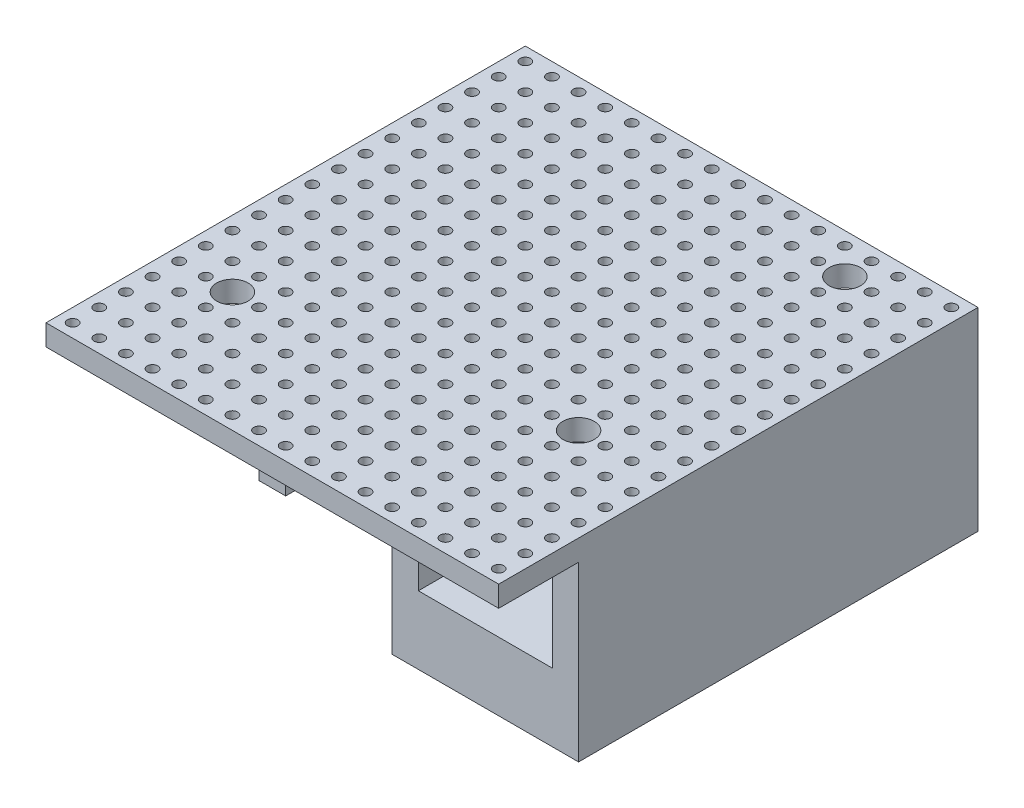
SolidWorks part; units mm, degrees
ref_plane "Front Plane" through (0, 0, 0) normal (0, 0, 1) x (1, 0, 0)
ref_plane "Top Plane" through (0, 0, 0) normal (0, 1, 0) x (1, 0, 0)
ref_plane "Right Plane" through (0, 0, 0) normal (1, 0, 0) x (0, 0, -1)
sketch "Sketch1" plane through (0, 0, 0) normal (0, 1, 0) x (1, 0, 0)
  line L1 (-28.6326, 15.7481) -> (34.8674, 15.7481)
  line L2 (-28.6326, 15.7481) -> (-28.6326, -29.9719)
  line L3 (-28.6326, -29.9719) -> (34.8674, -29.9719)
  line L4 (34.8674, 15.7481) -> (34.8674, -29.9719)
  circle A0 centre (33.5974, -28.7019) radius 0.5
  circle A1 centre (31.0574, -28.7019) radius 0.5
  circle A2 centre (28.5174, -28.7019) radius 0.5
  circle A3 centre (25.9774, -28.7019) radius 0.5
  circle A4 centre (23.4374, -28.7019) radius 0.5
  circle A5 centre (20.8974, -28.7019) radius 0.5
  circle A6 centre (18.3574, -28.7019) radius 0.5
  circle A7 centre (15.8174, -28.7019) radius 0.5
  circle A8 centre (13.2774, -28.7019) radius 0.5
  circle A9 centre (10.7374, -28.7019) radius 0.5
  circle A10 centre (8.1974, -28.7019) radius 0.5
  circle A11 centre (5.6574, -28.7019) radius 0.5
  circle A12 centre (3.1174, -28.7019) radius 0.5
  circle A13 centre (0.5774, -28.7019) radius 0.5
  circle A14 centre (-1.9626, -28.7019) radius 0.5
  circle A15 centre (-4.5026, -28.7019) radius 0.5
  circle A16 centre (-7.0426, -28.7019) radius 0.5
  circle A17 centre (-9.5826, -28.7019) radius 0.5
  circle A18 centre (-12.1226, -28.7019) radius 0.5
  circle A19 centre (-14.6626, -28.7019) radius 0.5
  circle A20 centre (-17.2026, -28.7019) radius 0.5
  circle A21 centre (-19.7426, -28.7019) radius 0.5
  circle A22 centre (-22.2826, -28.7019) radius 0.5
  circle A23 centre (-24.8226, -28.7019) radius 0.5
  circle A24 centre (-27.3626, -28.7019) radius 0.5
  circle A25 centre (31.0574, -26.1619) radius 0.5
  circle A26 centre (28.5174, -26.1619) radius 0.5
  circle A27 centre (25.9774, -26.1619) radius 0.5
  circle A28 centre (23.4374, -26.1619) radius 0.5
  circle A29 centre (20.8974, -26.1619) radius 0.5
  circle A30 centre (18.3574, -26.1619) radius 0.5
  circle A31 centre (15.8174, -26.1619) radius 0.5
  circle A32 centre (13.2774, -26.1619) radius 0.5
  circle A33 centre (10.7374, -26.1619) radius 0.5
  circle A34 centre (8.1974, -26.1619) radius 0.5
  circle A35 centre (5.6574, -26.1619) radius 0.5
  circle A36 centre (3.1174, -26.1619) radius 0.5
  circle A37 centre (0.5774, -26.1619) radius 0.5
  circle A38 centre (-1.9626, -26.1619) radius 0.5
  circle A39 centre (-4.5026, -26.1619) radius 0.5
  circle A40 centre (-7.0426, -26.1619) radius 0.5
  circle A41 centre (-9.5826, -26.1619) radius 0.5
  circle A42 centre (-12.1226, -26.1619) radius 0.5
  circle A43 centre (-14.6626, -26.1619) radius 0.5
  circle A44 centre (-17.2026, -26.1619) radius 0.5
  circle A45 centre (-19.7426, -26.1619) radius 0.5
  circle A46 centre (-22.2826, -26.1619) radius 0.5
  circle A47 centre (-24.8226, -26.1619) radius 0.5
  circle A48 centre (-27.3626, -26.1619) radius 0.5
  circle A49 centre (31.0574, -23.6219) radius 0.5
  circle A50 centre (28.5174, -23.6219) radius 0.5
  circle A51 centre (25.9774, -23.6219) radius 0.5
  circle A52 centre (23.4374, -23.6219) radius 0.5
  circle A53 centre (20.8974, -23.6219) radius 0.5
  circle A54 centre (18.3574, -23.6219) radius 0.5
  circle A55 centre (15.8174, -23.6219) radius 0.5
  circle A56 centre (13.2774, -23.6219) radius 0.5
  circle A57 centre (10.7374, -23.6219) radius 0.5
  circle A58 centre (8.1974, -23.6219) radius 0.5
  circle A59 centre (5.6574, -23.6219) radius 0.5
  circle A60 centre (3.1174, -23.6219) radius 0.5
  circle A61 centre (0.5774, -23.6219) radius 0.5
  circle A62 centre (-1.9626, -23.6219) radius 0.5
  circle A63 centre (-4.5026, -23.6219) radius 0.5
  circle A64 centre (-7.0426, -23.6219) radius 0.5
  circle A65 centre (-9.5826, -23.6219) radius 0.5
  circle A66 centre (-12.1226, -23.6219) radius 0.5
  circle A67 centre (-14.6626, -23.6219) radius 0.5
  circle A68 centre (-17.2026, -23.6219) radius 0.5
  circle A69 centre (-19.7426, -23.6219) radius 0.5
  circle A70 centre (-22.2826, -23.6219) radius 0.5
  circle A71 centre (-24.8226, -23.6219) radius 0.5
  circle A72 centre (-27.3626, -23.6219) radius 0.5
  circle A73 centre (31.0574, -21.0819) radius 0.5
  circle A74 centre (28.5174, -21.0819) radius 0.5
  circle A75 centre (25.9774, -21.0819) radius 0.5
  circle A76 centre (23.4374, -21.0819) radius 0.5
  circle A77 centre (20.8974, -21.0819) radius 0.5
  circle A78 centre (18.3574, -21.0819) radius 0.5
  circle A79 centre (15.8174, -21.0819) radius 0.5
  circle A80 centre (13.2774, -21.0819) radius 0.5
  circle A81 centre (10.7374, -21.0819) radius 0.5
  circle A82 centre (8.1974, -21.0819) radius 0.5
  circle A83 centre (5.6574, -21.0819) radius 0.5
  circle A84 centre (3.1174, -21.0819) radius 0.5
  circle A85 centre (0.5774, -21.0819) radius 0.5
  circle A86 centre (-1.9626, -21.0819) radius 0.5
  circle A87 centre (-4.5026, -21.0819) radius 0.5
  circle A88 centre (-7.0426, -21.0819) radius 0.5
  circle A89 centre (-9.5826, -21.0819) radius 0.5
  circle A90 centre (-12.1226, -21.0819) radius 0.5
  circle A91 centre (-14.6626, -21.0819) radius 0.5
  circle A92 centre (-17.2026, -21.0819) radius 0.5
  circle A93 centre (-19.7426, -21.0819) radius 0.5
  circle A94 centre (-22.2826, -21.0819) radius 0.5
  circle A95 centre (-24.8226, -21.0819) radius 0.5
  circle A96 centre (-27.3626, -21.0819) radius 0.5
  circle A97 centre (31.0574, -18.5419) radius 0.5
  circle A98 centre (28.5174, -18.5419) radius 0.5
  circle A99 centre (25.9774, -18.5419) radius 0.5
  circle A100 centre (23.4374, -18.5419) radius 0.5
  circle A101 centre (20.8974, -18.5419) radius 0.5
  circle A102 centre (18.3574, -18.5419) radius 0.5
  circle A103 centre (15.8174, -18.5419) radius 0.5
  circle A104 centre (13.2774, -18.5419) radius 0.5
  circle A105 centre (10.7374, -18.5419) radius 0.5
  circle A106 centre (8.1974, -18.5419) radius 0.5
  circle A107 centre (5.6574, -18.5419) radius 0.5
  circle A108 centre (3.1174, -18.5419) radius 0.5
  circle A109 centre (0.5774, -18.5419) radius 0.5
  circle A110 centre (-1.9626, -18.5419) radius 0.5
  circle A111 centre (-4.5026, -18.5419) radius 0.5
  circle A112 centre (-7.0426, -18.5419) radius 0.5
  circle A113 centre (-9.5826, -18.5419) radius 0.5
  circle A114 centre (-12.1226, -18.5419) radius 0.5
  circle A115 centre (-14.6626, -18.5419) radius 0.5
  circle A116 centre (-17.2026, -18.5419) radius 0.5
  circle A117 centre (-19.7426, -18.5419) radius 0.5
  circle A118 centre (-22.2826, -18.5419) radius 0.5
  circle A119 centre (-24.8226, -18.5419) radius 0.5
  circle A120 centre (-27.3626, -18.5419) radius 0.5
  circle A121 centre (31.0574, -16.0019) radius 0.5
  circle A122 centre (28.5174, -16.0019) radius 0.5
  circle A123 centre (25.9774, -16.0019) radius 0.5
  circle A124 centre (23.4374, -16.0019) radius 0.5
  circle A125 centre (20.8974, -16.0019) radius 0.5
  circle A126 centre (18.3574, -16.0019) radius 0.5
  circle A127 centre (15.8174, -16.0019) radius 0.5
  circle A128 centre (13.2774, -16.0019) radius 0.5
  circle A129 centre (10.7374, -16.0019) radius 0.5
  circle A130 centre (8.1974, -16.0019) radius 0.5
  circle A131 centre (5.6574, -16.0019) radius 0.5
  circle A132 centre (3.1174, -16.0019) radius 0.5
  circle A133 centre (0.5774, -16.0019) radius 0.5
  circle A134 centre (-1.9626, -16.0019) radius 0.5
  circle A135 centre (-4.5026, -16.0019) radius 0.5
  circle A136 centre (-7.0426, -16.0019) radius 0.5
  circle A137 centre (-9.5826, -16.0019) radius 0.5
  circle A138 centre (-12.1226, -16.0019) radius 0.5
  circle A139 centre (-14.6626, -16.0019) radius 0.5
  circle A140 centre (-17.2026, -16.0019) radius 0.5
  circle A141 centre (-19.7426, -16.0019) radius 0.5
  circle A142 centre (-22.2826, -16.0019) radius 0.5
  circle A143 centre (-24.8226, -16.0019) radius 0.5
  circle A144 centre (-27.3626, -16.0019) radius 0.5
  circle A145 centre (31.0574, -13.4619) radius 0.5
  circle A146 centre (28.5174, -13.4619) radius 0.5
  circle A147 centre (25.9774, -13.4619) radius 0.5
  circle A148 centre (23.4374, -13.4619) radius 0.5
  circle A149 centre (20.8974, -13.4619) radius 0.5
  circle A150 centre (18.3574, -13.4619) radius 0.5
  circle A151 centre (15.8174, -13.4619) radius 0.5
  circle A152 centre (13.2774, -13.4619) radius 0.5
  circle A153 centre (10.7374, -13.4619) radius 0.5
  circle A154 centre (8.1974, -13.4619) radius 0.5
  circle A155 centre (5.6574, -13.4619) radius 0.5
  circle A156 centre (3.1174, -13.4619) radius 0.5
  circle A157 centre (0.5774, -13.4619) radius 0.5
  circle A158 centre (-1.9626, -13.4619) radius 0.5
  circle A159 centre (-4.5026, -13.4619) radius 0.5
  circle A160 centre (-7.0426, -13.4619) radius 0.5
  circle A161 centre (-9.5826, -13.4619) radius 0.5
  circle A162 centre (-12.1226, -13.4619) radius 0.5
  circle A163 centre (-14.6626, -13.4619) radius 0.5
  circle A164 centre (-17.2026, -13.4619) radius 0.5
  circle A165 centre (-19.7426, -13.4619) radius 0.5
  circle A166 centre (-22.2826, -13.4619) radius 0.5
  circle A167 centre (-24.8226, -13.4619) radius 0.5
  circle A168 centre (-27.3626, -13.4619) radius 0.5
  circle A169 centre (31.0574, -10.9219) radius 0.5
  circle A170 centre (28.5174, -10.9219) radius 0.5
  circle A171 centre (25.9774, -10.9219) radius 0.5
  circle A172 centre (23.4374, -10.9219) radius 0.5
  circle A173 centre (20.8974, -10.9219) radius 0.5
  circle A174 centre (18.3574, -10.9219) radius 0.5
  circle A175 centre (15.8174, -10.9219) radius 0.5
  circle A176 centre (13.2774, -10.9219) radius 0.5
  circle A177 centre (10.7374, -10.9219) radius 0.5
  circle A178 centre (8.1974, -10.9219) radius 0.5
  circle A179 centre (5.6574, -10.9219) radius 0.5
  circle A180 centre (3.1174, -10.9219) radius 0.5
  circle A181 centre (0.5774, -10.9219) radius 0.5
  circle A182 centre (-1.9626, -10.9219) radius 0.5
  circle A183 centre (-4.5026, -10.9219) radius 0.5
  circle A184 centre (-7.0426, -10.9219) radius 0.5
  circle A185 centre (-9.5826, -10.9219) radius 0.5
  circle A186 centre (-12.1226, -10.9219) radius 0.5
  circle A187 centre (-14.6626, -10.9219) radius 0.5
  circle A188 centre (-17.2026, -10.9219) radius 0.5
  circle A189 centre (-19.7426, -10.9219) radius 0.5
  circle A190 centre (-22.2826, -10.9219) radius 0.5
  circle A191 centre (-24.8226, -10.9219) radius 0.5
  circle A192 centre (-27.3626, -10.9219) radius 0.5
  circle A193 centre (31.0574, -8.3819) radius 0.5
  circle A194 centre (28.5174, -8.3819) radius 0.5
  circle A195 centre (25.9774, -8.3819) radius 0.5
  circle A196 centre (23.4374, -8.3819) radius 0.5
  circle A197 centre (20.8974, -8.3819) radius 0.5
  circle A198 centre (18.3574, -8.3819) radius 0.5
  circle A199 centre (15.8174, -8.3819) radius 0.5
  circle A200 centre (13.2774, -8.3819) radius 0.5
  circle A201 centre (10.7374, -8.3819) radius 0.5
  circle A202 centre (8.1974, -8.3819) radius 0.5
  circle A203 centre (5.6574, -8.3819) radius 0.5
  circle A204 centre (3.1174, -8.3819) radius 0.5
  circle A205 centre (0.5774, -8.3819) radius 0.5
  circle A206 centre (-1.9626, -8.3819) radius 0.5
  circle A207 centre (-4.5026, -8.3819) radius 0.5
  circle A208 centre (-7.0426, -8.3819) radius 0.5
  circle A209 centre (-9.5826, -8.3819) radius 0.5
  circle A210 centre (-12.1226, -8.3819) radius 0.5
  circle A211 centre (-14.6626, -8.3819) radius 0.5
  circle A212 centre (-17.2026, -8.3819) radius 0.5
  circle A213 centre (-19.7426, -8.3819) radius 0.5
  circle A214 centre (-22.2826, -8.3819) radius 0.5
  circle A215 centre (-24.8226, -8.3819) radius 0.5
  circle A216 centre (-27.3626, -8.3819) radius 0.5
  circle A217 centre (31.0574, -5.8419) radius 0.5
  circle A218 centre (28.5174, -5.8419) radius 0.5
  circle A219 centre (25.9774, -5.8419) radius 0.5
  circle A220 centre (23.4374, -5.8419) radius 0.5
  circle A221 centre (20.8974, -5.8419) radius 0.5
  circle A222 centre (18.3574, -5.8419) radius 0.5
  circle A223 centre (15.8174, -5.8419) radius 0.5
  circle A224 centre (13.2774, -5.8419) radius 0.5
  circle A225 centre (10.7374, -5.8419) radius 0.5
  circle A226 centre (8.1974, -5.8419) radius 0.5
  circle A227 centre (5.6574, -5.8419) radius 0.5
  circle A228 centre (3.1174, -5.8419) radius 0.5
  circle A229 centre (0.5774, -5.8419) radius 0.5
  circle A230 centre (-1.9626, -5.8419) radius 0.5
  circle A231 centre (-4.5026, -5.8419) radius 0.5
  circle A232 centre (-7.0426, -5.8419) radius 0.5
  circle A233 centre (-9.5826, -5.8419) radius 0.5
  circle A234 centre (-12.1226, -5.8419) radius 0.5
  circle A235 centre (-14.6626, -5.8419) radius 0.5
  circle A236 centre (-17.2026, -5.8419) radius 0.5
  circle A237 centre (-19.7426, -5.8419) radius 0.5
  circle A238 centre (-22.2826, -5.8419) radius 0.5
  circle A239 centre (-24.8226, -5.8419) radius 0.5
  circle A240 centre (-27.3626, -5.8419) radius 0.5
  circle A241 centre (31.0574, -3.3019) radius 0.5
  circle A242 centre (28.5174, -3.3019) radius 0.5
  circle A243 centre (25.9774, -3.3019) radius 0.5
  circle A244 centre (23.4374, -3.3019) radius 0.5
  circle A245 centre (20.8974, -3.3019) radius 0.5
  circle A246 centre (18.3574, -3.3019) radius 0.5
  circle A247 centre (15.8174, -3.3019) radius 0.5
  circle A248 centre (13.2774, -3.3019) radius 0.5
  circle A249 centre (10.7374, -3.3019) radius 0.5
  circle A250 centre (8.1974, -3.3019) radius 0.5
  circle A251 centre (5.6574, -3.3019) radius 0.5
  circle A252 centre (3.1174, -3.3019) radius 0.5
  circle A253 centre (0.5774, -3.3019) radius 0.5
  circle A254 centre (-1.9626, -3.3019) radius 0.5
  circle A255 centre (-4.5026, -3.3019) radius 0.5
  circle A256 centre (-7.0426, -3.3019) radius 0.5
  circle A257 centre (-9.5826, -3.3019) radius 0.5
  circle A258 centre (-12.1226, -3.3019) radius 0.5
  circle A259 centre (-14.6626, -3.3019) radius 0.5
  circle A260 centre (-17.2026, -3.3019) radius 0.5
  circle A261 centre (-19.7426, -3.3019) radius 0.5
  circle A262 centre (-22.2826, -3.3019) radius 0.5
  circle A263 centre (-24.8226, -3.3019) radius 0.5
  circle A264 centre (-27.3626, -3.3019) radius 0.5
  circle A265 centre (31.0574, -0.7619) radius 0.5
  circle A266 centre (28.5174, -0.7619) radius 0.5
  circle A267 centre (25.9774, -0.7619) radius 0.5
  circle A268 centre (23.4374, -0.7619) radius 0.5
  circle A269 centre (20.8974, -0.7619) radius 0.5
  circle A270 centre (18.3574, -0.7619) radius 0.5
  circle A271 centre (15.8174, -0.7619) radius 0.5
  circle A272 centre (13.2774, -0.7619) radius 0.5
  circle A273 centre (10.7374, -0.7619) radius 0.5
  circle A274 centre (8.1974, -0.7619) radius 0.5
  circle A275 centre (5.6574, -0.7619) radius 0.5
  circle A276 centre (3.1174, -0.7619) radius 0.5
  circle A277 centre (0.5774, -0.7619) radius 0.5
  circle A278 centre (-1.9626, -0.7619) radius 0.5
  circle A279 centre (-4.5026, -0.7619) radius 0.5
  circle A280 centre (-7.0426, -0.7619) radius 0.5
  circle A281 centre (-9.5826, -0.7619) radius 0.5
  circle A282 centre (-12.1226, -0.7619) radius 0.5
  circle A283 centre (-14.6626, -0.7619) radius 0.5
  circle A284 centre (-17.2026, -0.7619) radius 0.5
  circle A285 centre (-19.7426, -0.7619) radius 0.5
  circle A286 centre (-22.2826, -0.7619) radius 0.5
  circle A287 centre (-24.8226, -0.7619) radius 0.5
  circle A288 centre (-27.3626, -0.7619) radius 0.5
  circle A289 centre (31.0574, 1.7781) radius 0.5
  circle A290 centre (28.5174, 1.7781) radius 0.5
  circle A291 centre (25.9774, 1.7781) radius 0.5
  circle A292 centre (23.4374, 1.7781) radius 0.5
  circle A293 centre (20.8974, 1.7781) radius 0.5
  circle A294 centre (18.3574, 1.7781) radius 0.5
  circle A295 centre (15.8174, 1.7781) radius 0.5
  circle A296 centre (13.2774, 1.7781) radius 0.5
  circle A297 centre (10.7374, 1.7781) radius 0.5
  circle A298 centre (8.1974, 1.7781) radius 0.5
  circle A299 centre (5.6574, 1.7781) radius 0.5
  circle A300 centre (3.1174, 1.7781) radius 0.5
  circle A301 centre (0.5774, 1.7781) radius 0.5
  circle A302 centre (-1.9626, 1.7781) radius 0.5
  circle A303 centre (-4.5026, 1.7781) radius 0.5
  circle A304 centre (-7.0426, 1.7781) radius 0.5
  circle A305 centre (-9.5826, 1.7781) radius 0.5
  circle A306 centre (-12.1226, 1.7781) radius 0.5
  circle A307 centre (-14.6626, 1.7781) radius 0.5
  circle A308 centre (-17.2026, 1.7781) radius 0.5
  circle A309 centre (-19.7426, 1.7781) radius 0.5
  circle A310 centre (-22.2826, 1.7781) radius 0.5
  circle A311 centre (-24.8226, 1.7781) radius 0.5
  circle A312 centre (-27.3626, 1.7781) radius 0.5
  circle A313 centre (31.0574, 4.3181) radius 0.5
  circle A314 centre (28.5174, 4.3181) radius 0.5
  circle A315 centre (25.9774, 4.3181) radius 0.5
  circle A316 centre (23.4374, 4.3181) radius 0.5
  circle A317 centre (20.8974, 4.3181) radius 0.5
  circle A318 centre (18.3574, 4.3181) radius 0.5
  circle A319 centre (15.8174, 4.3181) radius 0.5
  circle A320 centre (13.2774, 4.3181) radius 0.5
  circle A321 centre (10.7374, 4.3181) radius 0.5
  circle A322 centre (8.1974, 4.3181) radius 0.5
  circle A323 centre (5.6574, 4.3181) radius 0.5
  circle A324 centre (3.1174, 4.3181) radius 0.5
  circle A325 centre (0.5774, 4.3181) radius 0.5
  circle A326 centre (-1.9626, 4.3181) radius 0.5
  circle A327 centre (-4.5026, 4.3181) radius 0.5
  circle A328 centre (-7.0426, 4.3181) radius 0.5
  circle A329 centre (-9.5826, 4.3181) radius 0.5
  circle A330 centre (-12.1226, 4.3181) radius 0.5
  circle A331 centre (-14.6626, 4.3181) radius 0.5
  circle A332 centre (-17.2026, 4.3181) radius 0.5
  circle A333 centre (-19.7426, 4.3181) radius 0.5
  circle A334 centre (-22.2826, 4.3181) radius 0.5
  circle A335 centre (-24.8226, 4.3181) radius 0.5
  circle A336 centre (-27.3626, 4.3181) radius 0.5
  circle A337 centre (31.0574, 6.8581) radius 0.5
  circle A338 centre (28.5174, 6.8581) radius 0.5
  circle A339 centre (25.9774, 6.8581) radius 0.5
  circle A340 centre (23.4374, 6.8581) radius 0.5
  circle A341 centre (20.8974, 6.8581) radius 0.5
  circle A342 centre (18.3574, 6.8581) radius 0.5
  circle A343 centre (15.8174, 6.8581) radius 0.5
  circle A344 centre (13.2774, 6.8581) radius 0.5
  circle A345 centre (10.7374, 6.8581) radius 0.5
  circle A346 centre (8.1974, 6.8581) radius 0.5
  circle A347 centre (5.6574, 6.8581) radius 0.5
  circle A348 centre (3.1174, 6.8581) radius 0.5
  circle A349 centre (0.5774, 6.8581) radius 0.5
  circle A350 centre (-1.9626, 6.8581) radius 0.5
  circle A351 centre (-4.5026, 6.8581) radius 0.5
  circle A352 centre (-7.0426, 6.8581) radius 0.5
  circle A353 centre (-9.5826, 6.8581) radius 0.5
  circle A354 centre (-12.1226, 6.8581) radius 0.5
  circle A355 centre (-14.6626, 6.8581) radius 0.5
  circle A356 centre (-17.2026, 6.8581) radius 0.5
  circle A357 centre (-19.7426, 6.8581) radius 0.5
  circle A358 centre (-22.2826, 6.8581) radius 0.5
  circle A359 centre (-24.8226, 6.8581) radius 0.5
  circle A360 centre (-27.3626, 6.8581) radius 0.5
  circle A361 centre (31.0574, 9.3981) radius 0.5
  circle A362 centre (28.5174, 9.3981) radius 0.5
  circle A363 centre (25.9774, 9.3981) radius 0.5
  circle A364 centre (23.4374, 9.3981) radius 0.5
  circle A365 centre (20.8974, 9.3981) radius 0.5
  circle A366 centre (18.3574, 9.3981) radius 0.5
  circle A367 centre (15.8174, 9.3981) radius 0.5
  circle A368 centre (13.2774, 9.3981) radius 0.5
  circle A369 centre (10.7374, 9.3981) radius 0.5
  circle A370 centre (8.1974, 9.3981) radius 0.5
  circle A371 centre (5.6574, 9.3981) radius 0.5
  circle A372 centre (3.1174, 9.3981) radius 0.5
  circle A373 centre (0.5774, 9.3981) radius 0.5
  circle A374 centre (-1.9626, 9.3981) radius 0.5
  circle A375 centre (-4.5026, 9.3981) radius 0.5
  circle A376 centre (-7.0426, 9.3981) radius 0.5
  circle A377 centre (-9.5826, 9.3981) radius 0.5
  circle A378 centre (-12.1226, 9.3981) radius 0.5
  circle A379 centre (-14.6626, 9.3981) radius 0.5
  circle A380 centre (-17.2026, 9.3981) radius 0.5
  circle A381 centre (-19.7426, 9.3981) radius 0.5
  circle A382 centre (-22.2826, 9.3981) radius 0.5
  circle A383 centre (-24.8226, 9.3981) radius 0.5
  circle A384 centre (-27.3626, 9.3981) radius 0.5
  circle A385 centre (31.0574, 11.9381) radius 0.5
  circle A386 centre (28.5174, 11.9381) radius 0.5
  circle A387 centre (25.9774, 11.9381) radius 0.5
  circle A388 centre (23.4374, 11.9381) radius 0.5
  circle A389 centre (20.8974, 11.9381) radius 0.5
  circle A390 centre (18.3574, 11.9381) radius 0.5
  circle A391 centre (15.8174, 11.9381) radius 0.5
  circle A392 centre (13.2774, 11.9381) radius 0.5
  circle A393 centre (10.7374, 11.9381) radius 0.5
  circle A394 centre (8.1974, 11.9381) radius 0.5
  circle A395 centre (5.6574, 11.9381) radius 0.5
  circle A396 centre (3.1174, 11.9381) radius 0.5
  circle A397 centre (0.5774, 11.9381) radius 0.5
  circle A398 centre (-1.9626, 11.9381) radius 0.5
  circle A399 centre (-4.5026, 11.9381) radius 0.5
  circle A400 centre (-7.0426, 11.9381) radius 0.5
  circle A401 centre (-9.5826, 11.9381) radius 0.5
  circle A402 centre (-12.1226, 11.9381) radius 0.5
  circle A403 centre (-14.6626, 11.9381) radius 0.5
  circle A404 centre (-17.2026, 11.9381) radius 0.5
  circle A405 centre (-19.7426, 11.9381) radius 0.5
  circle A406 centre (-22.2826, 11.9381) radius 0.5
  circle A407 centre (-24.8226, 11.9381) radius 0.5
  circle A408 centre (-27.3626, 11.9381) radius 0.5
  circle A409 centre (33.5974, -26.1619) radius 0.5
  circle A410 centre (33.5974, -23.6219) radius 0.5
  circle A411 centre (33.5974, -21.0819) radius 0.5
  circle A412 centre (33.5974, -18.5419) radius 0.5
  circle A413 centre (33.5974, -16.0019) radius 0.5
  circle A414 centre (33.5974, -13.4619) radius 0.5
  circle A415 centre (33.5974, -10.9219) radius 0.5
  circle A416 centre (33.5974, -8.3819) radius 0.5
  circle A417 centre (33.5974, -5.8419) radius 0.5
  circle A418 centre (33.5974, -3.3019) radius 0.5
  circle A419 centre (33.5974, -0.7619) radius 0.5
  circle A420 centre (33.5974, 1.7781) radius 0.5
  circle A421 centre (33.5974, 4.3181) radius 0.5
  circle A422 centre (33.5974, 6.8581) radius 0.5
  circle A423 centre (33.5974, 9.3981) radius 0.5
  circle A424 centre (33.5974, 11.9381) radius 0.5
  circle A425 centre (33.5974, 14.4781) radius 0.5
  circle A426 centre (31.0574, 14.4781) radius 0.5
  circle A427 centre (28.5174, 14.4781) radius 0.5
  circle A428 centre (25.9774, 14.4781) radius 0.5
  circle A429 centre (23.4374, 14.4781) radius 0.5
  circle A430 centre (20.8974, 14.4781) radius 0.5
  circle A431 centre (18.3574, 14.4781) radius 0.5
  circle A432 centre (15.8174, 14.4781) radius 0.5
  circle A433 centre (13.2774, 14.4781) radius 0.5
  circle A434 centre (10.7374, 14.4781) radius 0.5
  circle A435 centre (8.1974, 14.4781) radius 0.5
  circle A436 centre (5.6574, 14.4781) radius 0.5
  circle A437 centre (3.1174, 14.4781) radius 0.5
  circle A438 centre (0.5774, 14.4781) radius 0.5
  circle A439 centre (-1.9626, 14.4781) radius 0.5
  circle A440 centre (-4.5026, 14.4781) radius 0.5
  circle A441 centre (-7.0426, 14.4781) radius 0.5
  circle A442 centre (-9.5826, 14.4781) radius 0.5
  circle A443 centre (-12.1226, 14.4781) radius 0.5
  circle A444 centre (-14.6626, 14.4781) radius 0.5
  circle A445 centre (-17.2026, 14.4781) radius 0.5
  circle A446 centre (-19.7426, 14.4781) radius 0.5
  circle A447 centre (-22.2826, 14.4781) radius 0.5
  circle A448 centre (-24.8226, 14.4781) radius 0.5
  circle A449 centre (-27.3626, 14.4781) radius 0.5
  dimension "D3" = 1
  dimension "D1" = 45.72
  dimension "D2" = 63.5
  dimension "D6" = 1.27
  dimension "D7" = 1.27
  dimension "D4" = 25
  dimension "D5" = 18
extrude "Boss-Extrude1" add sketch "Sketch1" along normal blind 2
sketch "Sketch2" plane through (0, 0, 0) normal (0, -1, 0) x (-1, 0, 0)
  line L0 (-34.8674, 15.7481) -> (28.6326, 15.7481) construction
  line L1 (3.2326, -22.3519) -> (-14.5474, -22.3519)
  line L2 (3.2326, -22.3519) -> (3.2326, 15.7481)
  line L3 (3.2326, 15.7481) -> (-14.5474, 15.7481)
  line L4 (-14.5474, -22.3519) -> (-14.5474, 15.7481)
  line L5 (28.6326, 15.7481) -> (28.6326, -29.9719) construction
  dimension "D1" = 25.4
  dimension "D2" = 17.78
  dimension "D3" = 38.1
extrude "Arduino Nano" add sketch "Sketch2" along normal blind 16.5
sketch "Sketch6" plane through (0, 0, -15.7481) normal (0, 0, -1) x (-1, 0, 0)
  line L0 (-14.5474, -16.5) -> (-14.5474, 0) construction
  line L1 (0.7326, 0) -> (-12.0474, 0)
  line L2 (0.7326, 0) -> (0.7326, -10)
  line L3 (0.7326, -10) -> (-12.0474, -10)
  line L4 (-12.0474, 0) -> (-12.0474, -10)
  line L5 (3.2326, -16.5) -> (3.2326, 0) construction
  line L6 (3.2326, 0) -> (28.6326, 0) construction
  dimension "D1" = 10
  dimension "D2" = 2.5
  dimension "D3" = 2.5
extrude "Cut-Extrude2" cut sketch "Sketch6" against normal through all both and the other way through all
sketch "Sketch3" plane through (0, 0, 0) normal (0, -1, 0) x (-1, 0, 0)
  line L1 (28.6326, 15.7481) -> (18.4726, 15.7481)
  line L2 (28.6326, 15.7481) -> (28.6326, -4.5719)
  line L3 (28.6326, -4.5719) -> (18.4726, -4.5719)
  line L4 (18.4726, 15.7481) -> (18.4726, -4.5719)
  dimension "D1" = 20.32
  dimension "D2" = 10.16
extrude "Relay" add sketch "Sketch3" along normal blind 11
sketch "Sketch4" plane through (0, 0, 0) normal (0, -1, 0) x (-1, 0, 0)
  line L0 (3.2326, 15.7481) -> (18.4726, 15.7481) construction
  line L1 (15.9326, 10.6681) -> (13.3926, 10.6681)
  line L2 (15.9326, 10.6681) -> (15.9326, 15.7481)
  line L3 (15.9326, 15.7481) -> (13.3926, 15.7481)
  line L4 (13.3926, 10.6681) -> (13.3926, 15.7481)
  line L5 (18.4726, 15.7481) -> (18.4726, -4.5719) construction
  line L6 (-34.8674, 15.7481) -> (-14.5474, 15.7481) construction
  line L7 (13.3926, 8.1281) -> (15.9326, 8.1281)
  line L8 (13.3926, 8.1281) -> (13.3926, -2.0319)
  line L9 (13.3926, -2.0319) -> (15.9326, -2.0319)
  line L10 (15.9326, 8.1281) -> (15.9326, -2.0319)
  line L11 (13.3926, -4.5719) -> (15.9326, -4.5719)
  line L12 (13.3926, -4.5719) -> (13.3926, -22.3519)
  line L13 (13.3926, -22.3519) -> (15.9326, -22.3519)
  line L14 (15.9326, -4.5719) -> (15.9326, -22.3519)
  line L15 (-19.6274, 8.1281) -> (-17.0874, 8.1281)
  line L16 (-19.6274, 8.1281) -> (-19.6274, 0.5081)
  line L17 (-19.6274, 0.5081) -> (-17.0874, 0.5081)
  line L18 (-17.0874, 8.1281) -> (-17.0874, 0.5081)
  line L19 (-14.5474, 15.7481) -> (-14.5474, -22.3519) construction
  line L20 (28.6326, -29.9719) -> (-34.8674, -29.9719) construction
  line L21 (-27.2474, 15.7481) -> (-24.7074, 15.7481)
  line L22 (-27.2474, 15.7481) -> (-27.2474, -2.0319)
  line L23 (-27.2474, -2.0319) -> (-24.7074, -2.0319)
  line L24 (-24.7074, 15.7481) -> (-24.7074, -2.0319)
  line L25 (-27.2474, -7.1119) -> (-24.7074, -7.1119)
  line L26 (-27.2474, -7.1119) -> (-27.2474, -29.9719)
  line L27 (-27.2474, -29.9719) -> (-24.7074, -29.9719)
  line L28 (-24.7074, -7.1119) -> (-24.7074, -29.9719)
  point P12 (14.6626, 8.1281)
  dimension "D1" = 2.54
  dimension "D2" = 5.08
  dimension "D3" = 2.54
  dimension "D4" = 10.16
  dimension "D5" = 2.54
  dimension "D6" = 2.54
  dimension "D7" = 17.78
  dimension "D8" = 2.54
  dimension "D9" = 7.62
  dimension "D10" = 2.54
  dimension "D11" = 7.62
  dimension "D12" = 2.54
  dimension "D13" = 17.78
  dimension "D14" = 2.54
  dimension "D15" = 5.08
  dimension "D16" = 22.86
extrude "Female Connectors" add sketch "Sketch4" along normal blind 8.5
sketch "Sketch5" plane through (0, 0, 0) normal (0, -1, 0) x (-1, 0, 0)
  circle A2 centre (22.2826, -18.5419) radius 1.5
  circle A3 centre (-5.6574, 11.9381) radius 1.5
  circle A4 centre (-5.6574, -13.4619) radius 1.5
  point P2 (0, 0)
  point P5 (-5.6574, -13.4619)
  point P7 (0, 0)
  point P11 (23.2984, -17.3626)
  point P12 (22.2826, -18.5419)
  dimension "D1" = 3
extrude "Mounting Holes" cut sketch "Sketch5" against normal blind 8.5
sketch "Sketch7" plane through (0, -8.5, 0) normal (0, -1, 0) x (-1, 0, 0)
  line L1 (-23.4374, -3.3019) -> (-43.7574, -3.3019)
  line L2 (-23.4374, -3.3019) -> (-23.4374, 19.5581)
  line L3 (-23.4374, 19.5581) -> (-43.7574, 19.5581)
  line L4 (-43.7574, -3.3019) -> (-43.7574, 19.5581)
  line L5 (-27.2474, 15.7481) -> (-27.2474, -2.0319) construction
  line L7 (-27.2474, -2.0319) -> (-24.7074, -2.0319) construction
  dimension "D1" = 22.86
  dimension "D2" = 20.32
  dimension "D3" = 1.27
  dimension "D4" = 3.81
extrude "LSM303" add sketch "Sketch7" along normal blind 2
sketch "Sketch8" plane through (0, -8.5, 0) normal (0, -1, 0) x (1, 0, 0)
  line L0 (24.7074, 29.9719) -> (24.7074, 7.1119) construction
  line L1 (26.9934, 33.7819) -> (28.0094, 33.7819)
  line L2 (24.4534, 31.2419) -> (24.4534, 5.8419)
  line L3 (26.9934, 3.3019) -> (28.0094, 3.3019)
  line L4 (43.5034, 31.2419) -> (43.5034, 5.8419)
  line L9 (28.0094, 5.8419) -> (28.0094, 31.2419) construction
  line L10 (40.9634, 5.8419) -> (28.0094, 5.8419) construction
  line L11 (38.4234, 5.8419) -> (30.5494, 5.8419)
  line L12 (38.4234, 31.2419) -> (30.5494, 31.2419)
  arc A0 (38.4234, 5.8419) -> (43.5034, 5.8419) centre (40.9634, 5.8419) ccw
  arc A1 (43.5034, 31.2419) -> (38.4234, 31.2419) centre (40.9634, 31.2419) ccw
  arc A2 (30.5494, 31.2419) -> (28.0094, 33.7819) centre (28.0094, 31.2419) ccw
  arc A3 (28.0094, 3.3019) -> (30.5494, 5.8419) centre (28.0094, 5.8419) ccw
  arc A5 (26.9934, 33.7819) -> (24.4534, 31.2419) centre (26.9934, 31.2419) ccw
  arc A6 (26.9934, 3.3019) -> (24.4534, 5.8419) centre (26.9934, 5.8419) cw
  dimension "D4" = 5.08
  dimension "D5" = 5.08
  dimension "D7" = 5.08
  dimension "D8" = 5.08
  dimension "D9" = 2.54
  dimension "D10" = 2.54
  dimension "D1" = 19.05
  dimension "D2" = 0.254
  dimension "D3" = 30.48
  dimension "D6" = 3.556
extrude "Gyro" add sketch "Sketch8" along normal blind 2 separate body
sketch "Sketch9" plane through (0, 0, 0) normal (0, -1, 0) x (-1, 0, 0)
  line L1 (-14.5474, 26.9069) -> (-46.8679, 26.9069)
  line L2 (-14.5474, 26.9069) -> (-14.5474, -38.6789)
  line L3 (-14.5474, -38.6789) -> (-46.8679, -38.6789)
  line L4 (-46.8679, 26.9069) -> (-46.8679, -38.6789)
  point P5 (0, 0)
extrude "Cut-Extrude3" cut sketch "Sketch9" against normal through all both and the other way through all
